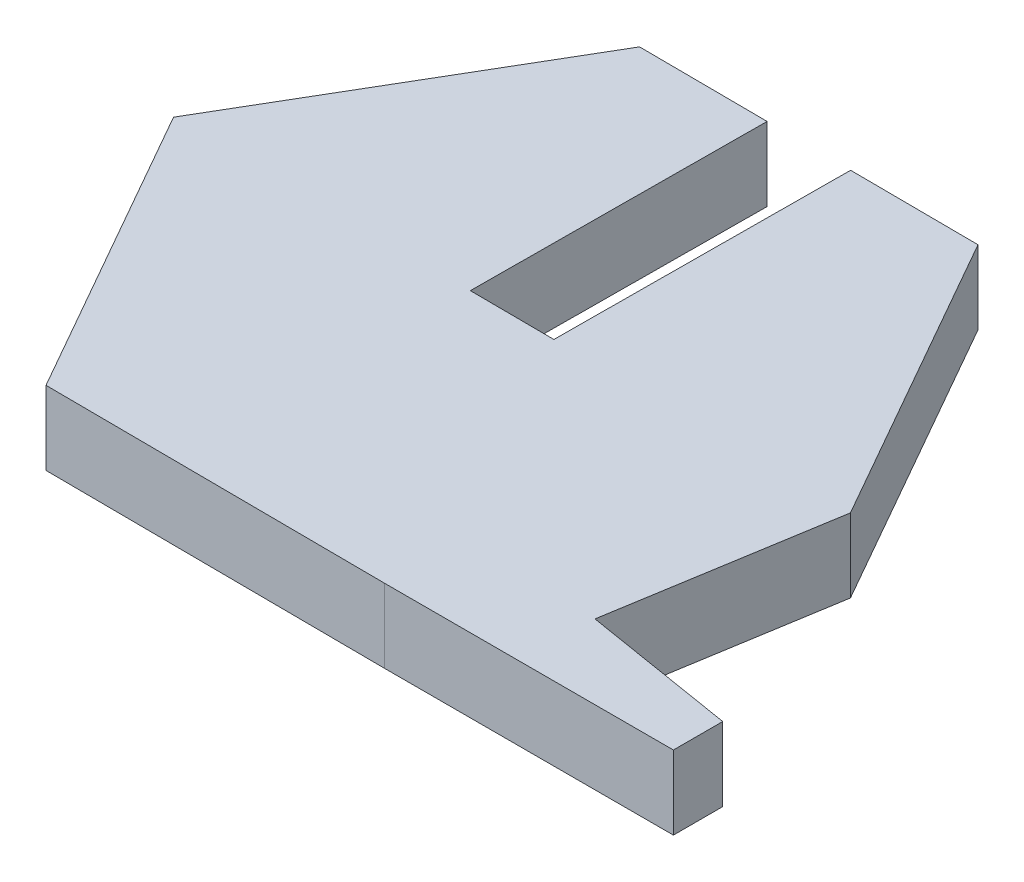
SolidWorks part; units mm, degrees
ref_plane "Front Plane" through (0, 0, 0) normal (0, 0, 1) x (1, 0, 0)
ref_plane "Top Plane" through (0, 0, 0) normal (0, 1, 0) x (1, 0, 0)
ref_plane "Right Plane" through (0, 0, 0) normal (1, 0, 0) x (0, 0, -1)
sketch "Sketch1" plane through (0, 0, 0) normal (0, 1, 0) x (1, 0, 0)
  line L0 (11.5468, -0.0722) -> (10.3299, -7.5164)
  line L2 (11.5468, -0.0722) -> (5.836, 9.9637)
  line L3 (5.836, 9.9637) -> (-5.7108, 10.0359)
  line L4 (-5.7108, 10.0359) -> (-11.5468, 0.0722)
  line L5 (-11.5468, 0.0722) -> (-5.836, -9.9637)
  line L6 (-5.836, -9.9637) -> (5.7108, -10.0359)
  line L7 (10.3299, -7.5164) -> (15.5082, -8.363)
  line L8 (15.5082, -8.363) -> (15.5082, -10.0359)
  line L9 (15.5082, -10.0359) -> (5.7108, -10.0359)
  line L11 (5.7108, -10.0359) -> (11.5468, -0.0722) [skipped]
  circle A0 centre (0, 0) radius 10 construction
  dimension "D1" = 20
extrude "Boss-Extrude1" add sketch "Sketch1" along normal blind 2.5
sketch "Sketch8" plane through (0.0626, 0, -9.9998) normal (0.0063, 0, -1) x (-1, 0, -0.0063)
  line L0 (-5.7735, 2.5) -> (5.7735, 2.5) construction
  line L1 (1.422, 2.5) -> (-1.428, 2.5)
  line L2 (1.422, 2.5) -> (1.422, 0)
  line L3 (1.422, 0) -> (-1.428, 0)
  line L4 (-1.428, 2.5) -> (-1.428, 0)
  line L5 (-5.7735, 0) -> (5.7735, 0) construction
  dimension "D1" = 2.85
  dimension "D2" = 10.125
extrude "Cut-Extrude1" cut sketch "Sketch8" against normal blind 10
